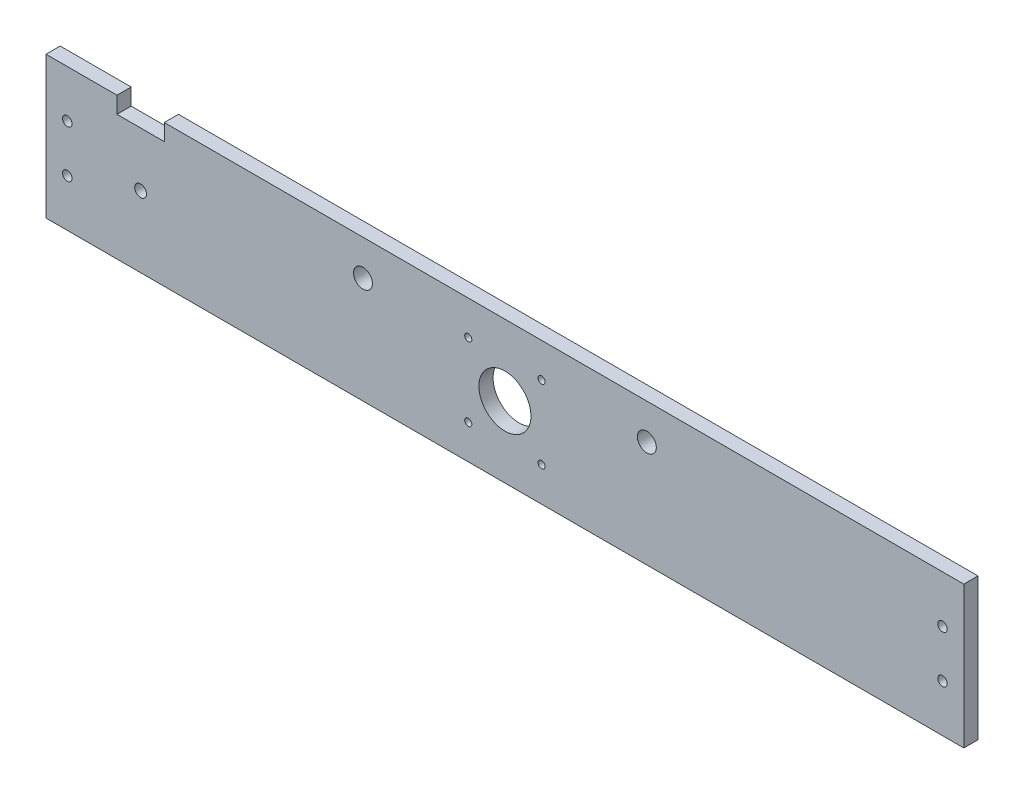
SolidWorks part; units mm, degrees
material "Acrylic (Medium-high impact)"
ref_plane "Front Plane" through (0, 0, 0) normal (0, 0, 1) x (1, 0, 0)
ref_plane "Top Plane" through (0, 0, 0) normal (0, 1, 0) x (1, 0, 0)
ref_plane "Right Plane" through (0, 0, 0) normal (1, 0, 0) x (0, 0, -1)
sketch "Sketch1" plane through (0, 0, 0) normal (0, 0, 1) x (1, 0, 0)
  line L0 (0, -1000) -> (0, 49000) construction
  line L1 (-194, -30) -> (194, -30)
  line L3 (-194, 30) -> (194, 30)
  line L7 (-1000, 0) -> (49000, 0) construction
  line L8 (194, 30) -> (194, -30)
  line L17 (-164, 30) -> (-144, 30)
  line L18 (-164, 30) -> (-164, 23)
  line L19 (-164, 23) -> (-144, 23)
  line L20 (-194, 30) -> (-194, -30)
  line L25 (-1145.7551, 15) -> (48854.2449, 15) construction
  line L26 (-144, 30) -> (-144, 23)
  circle A1 centre (60, 15) radius 4
  circle A2 centre (-60, 15) radius 4
  circle A11 centre (0, 0) radius 11
  circle A12 centre (185, 10) radius 2
  circle A13 centre (185, -10) radius 2
  circle A14 centre (-185, -10) radius 2
  circle A15 centre (-185, 10) radius 2
  circle A16 centre (-154, 0) radius 2.5
  point P0 (0, 0)
  dimension "D7" = 9
  dimension "D8" = 8
  dimension "D9" = 8
  dimension "D10" = 60
  dimension "D11" = 60
  dimension "D4" = 194
  dimension "D15" = 30
  dimension "D5" = 22
  dimension "D6" = 4
  dimension "D12" = 20
  dimension "D16" = 5
  dimension "D2" = 60
  dimension "D3" = 15
  dimension "D13" = 7
  dimension "D14" = 20
  dimension "D17" = 15
  dimension "D18" = 40
extrude "Boss-Extrude1" add sketch "Sketch1" along normal blind 6
sketch "Sketch2" plane through (0, 0, 6) normal (0, 0, 1) x (1, 0, 0)
  line L0 (-1000, 0) -> (49000, 0) construction
  line L1 (0, -1000) -> (0, 49000) construction
  circle A0 centre (15.495, 15.495) radius 1.5
  circle A4 centre (-15.495, 15.495) radius 1.5
  circle A5 centre (15.495, -15.495) radius 1.5
  circle A6 centre (-15.495, -15.495) radius 1.5
  dimension "D1" = 3
  dimension "D2" = 15.495
  dimension "D3" = 15.495
extrude "Cut-Extrude1" cut sketch "Sketch2" against normal up to next
